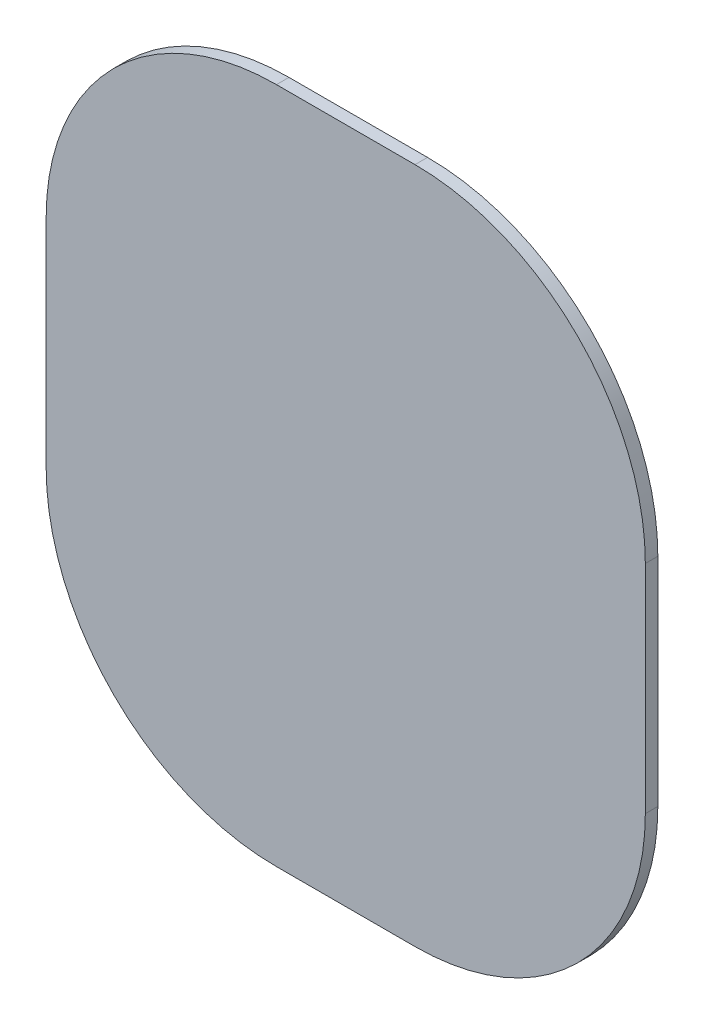
SolidWorks part; units mm, degrees
ref_plane "Front Plane" through (0, 0, 0) normal (0, 0, 1) x (1, 0, 0)
ref_plane "Top Plane" through (0, 0, 0) normal (0, 1, 0) x (1, 0, 0)
ref_plane "Right Plane" through (0, 0, 0) normal (1, 0, 0) x (0, 0, -1)
sketch "Sketch1" plane through (0, 0, 0) normal (0, 0, 1) x (1, 0, 0)
  line L53 (241.5433, 205.3413) -> (246.9652, 204.9327)
  line L72 (-6.9957, 198.2293) -> (-6.9957, -78.6307)
  line L73 (35.8033, 153.9063) -> (35.8033, -34.3077)
  line L74 (69.2043, 274.4293) -> (259.7043, 274.4293)
  line L75 (335.9043, 198.2293) -> (335.9043, -78.6307)
  line L76 (259.7043, -154.8307) -> (69.2043, -154.8307)
  line L77 (87.2383, 205.3413) -> (241.5433, 205.3413)
  line L78 (35.8033, 153.9063) -> (35.8033, -34.3077)
  line L79 (87.2383, -85.7427) -> (238.612, -85.7427)
  line L80 (292.9783, 152.6781) -> (292.9783, -34.3077)
  line L81 (87.2383, -85.7427) -> (238.612, -85.7427)
  line L82 (292.9783, -34.3077) -> (292.9783, 152.6781)
  line L83 (241.5433, 205.3413) -> (87.2383, 205.3413)
  line L84 (-6.9957, 198.2293) -> (-6.9957, -78.6307)
  line L85 (69.2043, -154.8307) -> (259.7043, -154.8307)
  line L86 (335.9043, -78.6307) -> (335.9043, 198.2293)
  line L87 (259.7043, 274.4293) -> (69.2043, 274.4293)
  arc A32 (35.8033, -34.3077) -> (87.2383, -85.7427) centre (87.2383, -34.3077) ccw
  arc A33 (238.612, -85.7427) -> (292.9783, -34.3077) centre (238.612, -31.2928) ccw
  arc A34 (292.9783, 152.6781) -> (241.5433, 205.3413) centre (240.3004, 152.6781) ccw
  arc A35 (87.2383, 205.3413) -> (35.8033, 153.9063) centre (87.2383, 153.9063) ccw
  arc A36 (-6.9957, -78.6307) -> (69.2043, -154.8307) centre (69.2043, -78.6307) ccw
  arc A37 (259.7043, -154.8307) -> (335.9043, -78.6307) centre (259.7043, -78.6307) ccw
  arc A38 (335.9043, 198.2293) -> (259.7043, 274.4293) centre (259.7043, 198.2293) ccw
  arc A39 (69.2043, 274.4293) -> (-6.9957, 198.2293) centre (69.2043, 198.2293) ccw
  point P7 (-1548.8445, 807.057)
  point P171 (69.2043, 274.4293)
  point P172 (259.7043, 274.4293)
  point P173 (335.9043, 198.2293)
  point P174 (335.9043, -78.6307)
  point P175 (87.2383, 205.3413)
  point P176 (241.5433, 205.3413)
  point P181 (292.9783, 152.6781)
  point P182 (292.9783, -34.3077)
  point P183 (241.5433, -85.7427)
  point P184 (87.2383, -85.7427)
  point P185 (35.8033, -34.3077)
  point P186 (35.8033, 153.9063)
  point P187 (259.7043, -154.8307)
  point P188 (69.2043, -154.8307)
  point P200 (-6.9957, -78.6307)
  point P202 (-6.9957, 198.2293)
ref_plane "Plane1" through (0, 0, 10.16) normal (0, 0, 1) x (1, 0, 0)
ref_plane "Plane2" through (0, 0, 8.89) normal (0, 0, 1) x (1, 0, 0)
sketch "Sketch14" plane through (0, 0, 8.89) normal (0, 0, 1) x (1, 0, 0)
  line L20 (198.2363, 213.4693) -> (127.9259, 213.4693)
  line L21 (11.0859, -13.2857) -> (11.0859, 96.6293)
  line L22 (198.2363, -130.1257) -> (127.9259, -130.1257)
  line L23 (315.0763, 96.6293) -> (315.0763, -13.2857)
  arc A8 (315.0763, 96.6293) -> (198.2363, 213.4693) centre (198.2363, 96.6293) ccw
  arc A9 (127.9259, 213.4693) -> (11.0859, 96.6293) centre (127.9259, 96.6293) ccw
  arc A10 (127.9259, -130.1257) -> (11.0859, -13.2857) centre (127.9259, -13.2857) cw
  arc A11 (315.0763, -13.2857) -> (198.2363, -130.1257) centre (198.2363, -13.2857) cw
extrude "Boss-Extrude3" add sketch "Sketch14" along normal blind 6.35
